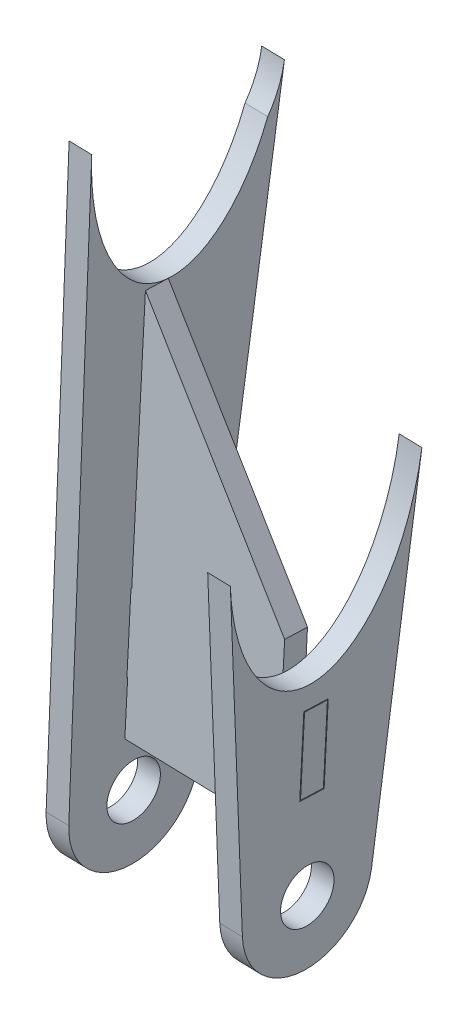
SolidWorks part; units mm, degrees
material "1.0545 (S355N)"
ref_plane "Płaszczyzna XY" through (0, 0, 0) normal (0, 0, 1) x (1, 0, 0)
ref_plane "Płaszczyzna XZ" through (0, 0, 0) normal (0, 1, 0) x (1, 0, 0)
ref_plane "Płaszczyzna YZ" through (0, 0, 0) normal (1, 0, 0) x (0, 0, -1)
ref_plane "Płaszczyzna1" through (10.1927, -0.2092, 0.0569) normal (0.9998, -0.0205, 0.0056) x (0.0056, -0.0001, -1)
sketch "Szkic1" plane through (10.1927, -0.2092, 0.0569) normal (0.9998, -0.0205, 0.0056) x (0.0056, -0.0001, -1)
  line L0 (-569.2155, -78.4997) -> (-571.6448, -36.8767)
  line L1 (-552.2947, -79.0513) -> (-546.6355, -33.4511)
  circle A0 centre (-560.7299, -78.0045) radius 3.5
  arc A1 (-569.2155, -78.4997) -> (-552.2947, -79.0513) centre (-560.7299, -78.0045) ccw
  circle A2 centre (-560.7299, -78.0045) radius 8.5 construction
  spline S1 degree 3 poles (-561.6178, -53.5323) (-586.442, -50.5726) (-581.2571, -7.0844) (-556.4329, -10.044) (-531.6087, -13.0037) (-536.7936, -56.492) (-561.6178, -53.5323) (-586.442, -50.5726) (-581.2571, -7.0844) knots -0.5 0 0 0 0.5 0.5 0.5 1 1 1 1.5 1.5 1.5 weights 1 0.333333 0.333333 1 0.333333 0.333333 1 0.333333 0.333333 only from (-561.6178, -53.5323) to (-561.6178, -53.5323)
  dimension "D1" = 7
  dimension "D2" = 5
extrude "Dodanie-wyciągnięcie1" add sketch "Szkic1" against normal blind 3 contours L1 S1 L0 A1 A0
ref_plane "Płaszczyzna2" through (-12.8021, 0.2628, -0.0715) normal (0.9998, -0.0205, 0.0056) x (0.0056, -0.0001, -1)
sketch "Szkic3" plane through (-12.8021, 0.2628, -0.0715) normal (0.9998, -0.0205, 0.0056) x (0.0056, -0.0001, -1)
  line L0 (-569.2284, -77.844) -> (-567.7821, -1.2366)
  line L1 (-552.2993, -79.0882) -> (-542.5172, -2.9897)
  circle A0 centre (-560.7299, -78.0045) radius 3.5
  circle A1 centre (-560.7299, -78.0045) radius 3.5 construction
  arc A2 (-569.2284, -77.844) -> (-552.2993, -79.0882) centre (-560.7299, -78.0045) ccw
  spline S1 degree 3 poles (-542.5172, -2.9897) (-542.7766, -5.0077) (-543.4829, -6.8769) (-544.5882, -8.5014) knots 0.307426 0.307426 0.307426 0.307426 1 1 1 1 weights 0.976444 0.966607 0.974459 1
  spline S3 degree 3 poles (-544.5882, -8.5014) (-553.2618, -32.5) (-568.2938, -28.3394) (-567.7821, -1.2366) knots 0 0 0 0 0.978693 0.978693 0.978693 0.978693 weights 1 0.514675 0.504334 0.968977
  dimension "D1" = 5
extrude "Dodanie-wyciągnięcie2" add sketch "Szkic3" against normal blind 3 separate body
sketch "Szkic4" plane through (7.1933, -0.1476, 0.0402) normal (-0.9998, 0.0205, -0.0056) x (-0.0056, 0.0001, 1)
  line L0 (560.7299, -78.0045) -> (559.9323, -53.5346) construction
  line L1 (559.9323, -53.5346) -> (570.6361, -54.1594) construction
  line L2 (569.2155, -78.4997) -> (571.6448, -36.8767) construction
  line L3 (559.9323, -53.5346) -> (549.2918, -54.8552) construction
  line L4 (552.2947, -79.0513) -> (546.6355, -33.4511) construction
  spline S1 degree 3 poles (546.6355, -33.4511) (548.4208, -47.8369) (555.4508, -54.2676) (561.6178, -53.5323) (566.5009, -52.9501) (571.0155, -47.6596) (571.6448, -36.8767) knots 0.751053 0.751053 0.751053 0.751053 1 1 1 1.211755 1.211755 1.211755 1.211755 weights 0.500009 0.501406 0.66807 1 0.71766 0.554894 0.511701 construction
ref_plane "Płaszczyzna3" through (-2.7398, 18.2369, 557.5859) normal (0.0049, -0.0327, -0.9995) x (0.0207, 0.9993, -0.0326)
sketch "Szkic5" plane through (-2.7398, 18.2369, 557.5859) normal (0.0049, -0.0327, -0.9995) x (0.0207, 0.9993, -0.0326)
  line L0 (-38.6447, -15.805) -> (-92.7324, -15.805)
  line L1 (-100.5403, -15.805) -> (-105.5403, -15.805)
  line L3 (-82.7324, -15.805) -> (-92.7324, -15.805)
  line L4 (-71.7496, 10.195) -> (-92.7324, 10.195)
  line L5 (-100.5403, 10.195) -> (-105.5403, 10.195)
  line L6 (-84.7324, 7.195) -> (-89.7324, 7.195)
  line L7 (-74.7324, 10.195) -> (-84.7324, 10.195)
  line L8 (-38.6447, -12.805) -> (-92.7324, -12.805)
  line L9 (-100.5403, -12.805) -> (-105.5403, -12.805)
  line L11 (-38.868, -12.805) -> (-72.7324, -12.805)
  line L16 (-68.0298, 7.195) -> (-38.868, -12.805)
  line L17 (-68.0298, 7.195) -> (-74.7324, 7.195)
  line L18 (-74.7324, 7.195) -> (-74.7324, 10.195)
  line L19 (-74.7324, 10.195) -> (-84.7324, 10.195)
  line L20 (-84.7324, 10.195) -> (-84.7324, 7.195)
  line L21 (-84.7324, 7.195) -> (-89.7324, 7.195)
  line L22 (-89.7324, 7.195) -> (-89.7324, -12.805)
  line L23 (-89.7324, -12.805) -> (-82.7324, -12.805)
  line L24 (-72.7324, -12.805) -> (-72.7324, -15.805)
  line L25 (-72.7324, -15.805) -> (-82.7324, -15.805)
  line L26 (-82.7324, -15.805) -> (-82.7324, -12.805)
  line L27 (-72.7324, -12.805) -> (-38.868, -12.805)
  line L28 (-82.7324, -12.805) -> (-89.7324, -12.805)
  line L45 (-97.0409, -12.805) -> (-20.664, -12.805) construction
  line L46 (-97.0039, 7.195) -> (-51.2434, 7.195) construction
  line L49 (-92.7324, -12.805) -> (-92.7324, 10.195) construction
  dimension "D1" = 10
  dimension "D2" = 5
  dimension "D3" = 3
  dimension "D4" = 21.7026
extrude "Dodanie-wyciągnięcie3" add sketch "Szkic5" along normal mid plane 3 separate body contours L26 L25 L24 L11 L16 L17 L18 L7 L20 L6 L22 L23
ref_plane "Płaszczyzna4" through (-20.2457, -64.1586, 558.6939) normal (-0.0207, -0.9993, 0.0326) x (-0.9998, 0.0207, -0.0007)
ref_plane "Płaszczyzna5" through (10.1927, -0.2092, 0.0569) normal (0.9998, -0.0205, 0.0056) x (0.0056, -0.0001, -1)
sketch "Szkic7" plane through (10.1927, -0.2092, 0.0569) normal (0.9998, -0.0205, 0.0056) x (0.0056, -0.0001, -1)
  line L0 (-561.5287, -56.467) -> (-561.8545, -66.4617)
  line L1 (-561.5287, -56.467) -> (-561.8545, -66.4617)
  line L2 (-558.5302, -56.5648) -> (-558.8561, -66.5595)
  line L3 (-558.5302, -56.5648) -> (-558.8561, -66.5595)
  line L4 (-561.8545, -66.4617) -> (-558.8561, -66.5595)
  line L5 (-561.5287, -56.467) -> (-558.5302, -56.5648)
sketch "Szkic8" plane through (10.1927, -0.2092, 0.0569) normal (0.9998, -0.0205, 0.0056) x (0.0056, -0.0001, -1)
  line L0 (-561.8545, -66.4617) -> (-561.5287, -56.467) construction
  line L1 (-561.5287, -56.467) -> (-558.5302, -56.5648) construction
  line L2 (-558.5302, -56.5648) -> (-558.8561, -66.5595) construction
  line L3 (-558.8561, -66.5595) -> (-561.8545, -66.4617) construction
  line L12 (-561.6253, -56.3638) -> (-561.9577, -66.5584)
  line L13 (-561.9577, -66.5584) -> (-558.7594, -66.6627)
  line L14 (-558.7594, -66.6627) -> (-558.427, -56.4681)
  line L15 (-558.427, -56.4681) -> (-561.6253, -56.3638)
  line L16 (-561.6253, -56.3638) -> (-561.9577, -66.5584)
  line L17 (-561.9577, -66.5584) -> (-558.7594, -66.6627)
  line L18 (-558.7594, -66.6627) -> (-558.427, -56.4681)
  line L19 (-558.427, -56.4681) -> (-561.6253, -56.3638)
  dimension "D1" = 0.1
extrude "Wytnij-wyciągnięcie2" cut sketch "Szkic8" along direction (0.9998, -0.0205, 0.0056) on the side against the normal through all contours L16 L17 L18 L19
sketch "Szkic9" plane through (-15.8015, 0.3243, -0.0883) normal (-0.9998, 0.0205, -0.0056) x (-0.0056, 0.0001, 1)
  line L0 (558.4651, -54.5658) -> (558.7909, -64.5605) construction
  line L1 (558.7909, -64.5605) -> (561.7893, -64.4628) construction
  line L2 (561.7893, -64.4628) -> (561.4635, -54.4681) construction
  line L3 (561.4635, -54.4681) -> (558.4651, -54.5658) construction
  line L4 (561.5602, -54.3649) -> (558.3619, -54.4692)
  line L5 (558.3619, -54.4692) -> (558.6942, -64.6637)
  line L6 (558.6942, -64.6637) -> (561.8925, -64.5595)
  line L7 (561.8925, -64.5595) -> (561.5602, -54.3649)
  dimension "D1" = 0.1
extrude "Wytnij-wyciągnięcie3" cut sketch "Szkic9" against normal blind 3
